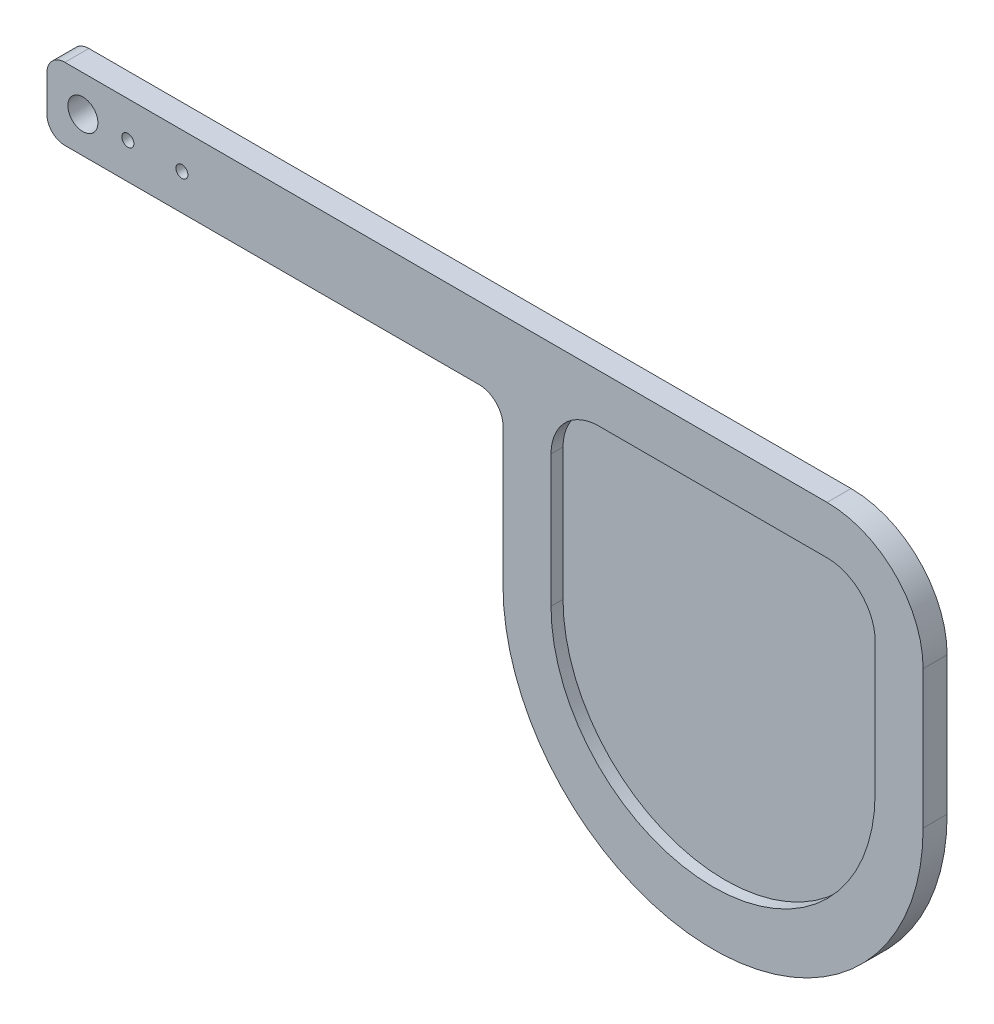
SolidWorks part; units mm, degrees
ref_plane "Спереди" through (0, 0, 0) normal (0, 0, 1) x (1, 0, 0)
ref_plane "Сверху" through (0, 0, 0) normal (0, 1, 0) x (1, 0, 0)
ref_plane "Справа" through (0, 0, 0) normal (1, 0, 0) x (0, 0, -1)
sketch "Эскиз1" plane through (0, 0, 0) normal (0, 0, 1) x (1, 0, 0)
  line L0 (3, 0) -> (72, 0)
  line L1 (76, -4) -> (76, -27)
  line L2 (146, -27) -> (146, -4)
  line L3 (130, 12) -> (3, 12)
  line L4 (0, 9) -> (0, 3)
  line L5 (0, 6) -> (142.49, 6) construction
  line L6 (111, -62) -> (40.2851, -62) construction
  line L7 (76, -4) -> (146, -4) construction
  arc A0 (72, 0) -> (76, -4) centre (72, -4) cw
  arc A1 (76, -27) -> (146, -27) centre (111, -27) ccw
  arc A2 (146, -4) -> (130, 12) centre (130, -4) ccw
  circle A3 centre (6, 6) radius 2.5
  circle A4 centre (13.5, 6) radius 1
  circle A5 centre (22.5, 6) radius 1
  arc A6 (3, 0) -> (0, 3) centre (3, 3) cw
  arc A7 (3, 12) -> (0, 9) centre (3, 9) ccw
  point P24 (0, 0)
  point P27 (0, 12)
  dimension "D1" = 12
  dimension "D2" = 6
  dimension "D3" = 140
  dimension "D6" = 4
  dimension "D7" = 5
  dimension "D10" = 2
  dimension "D11" = 3
  dimension "D4" = 70
  dimension "D5" = 62
  dimension "D8" = 7.5
  dimension "D9" = 9
extrude "Бобышка-Вытянуть1" add sketch "Эскиз1" along normal blind 4
sketch "Эскиз2" plane through (0, 0, 4) normal (0, 0, 1) x (1, 0, 0)
  line L0 (92, 4) -> (130, 4)
  line L1 (138, -4) -> (138, -26)
  line L2 (84, -26) -> (84, -4)
  line L3 (130, 12) -> (3, 12) construction
  line L4 (146, -27) -> (146, -4) construction
  line L5 (76, -4) -> (76, -27) construction
  line L6 (84, -26) -> (138, -26) construction
  arc A0 (130, 4) -> (138, -4) centre (130, -4) cw
  arc A1 (138, -26) -> (84, -26) centre (111, -26) cw
  arc A2 (92, 4) -> (84, -4) centre (92, -4) ccw
  dimension "D4" = 8
  dimension "D5" = 8
  dimension "D1" = 8
  dimension "D2" = 8
  dimension "D3" = 8
  dimension "D6" = 30
extrude "Вырез-Вытянуть1" cut sketch "Эскиз2" against normal blind 2
